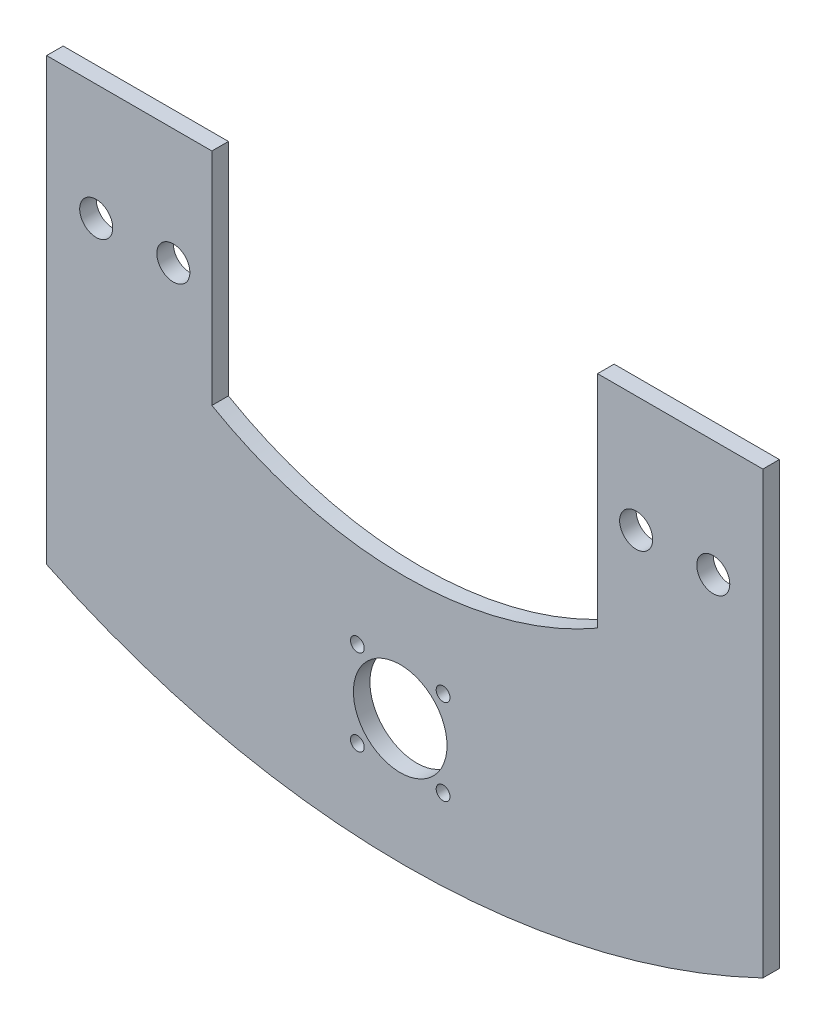
SolidWorks part; units mm, degrees
ref_plane "Front Plane" through (0, 0, 0) normal (0, 0, 1) x (1, 0, 0)
ref_plane "Top Plane" through (0, 0, 0) normal (0, 1, 0) x (1, 0, 0)
ref_plane "Right Plane" through (0, 0, 0) normal (1, 0, 0) x (0, 0, -1)
sketch "Sketch1" plane through (0, 0, 0) normal (0, 0, 1) x (1, 0, 0)
  line L1 (-34.1797, 1.6565) -> (-34.1797, 41.6565)
  line L2 (-34.1797, 41.6565) -> (-64.1797, 41.6565)
  line L3 (-64.1797, 41.6565) -> (-64.1797, -38.3435)
  line L5 (65.8203, -38.3435) -> (65.8203, 41.6565)
  line L6 (65.8203, 41.6565) -> (35.8203, 41.6565)
  line L7 (35.8203, 41.6565) -> (35.8203, 1.6565)
  arc A0 (-34.1797, 1.6565) -> (35.8203, 1.6565) centre (0.8203, 62.2783) ccw
  arc A1 (-64.1797, -38.3435) -> (65.8203, -38.3435) centre (0.8203, 96.8416) ccw
  circle A2 centre (56.8203, 20.5545) radius 3
  circle A3 centre (42.8203, 20.5545) radius 3
  circle A4 centre (-55.1797, 20.5545) radius 3
  circle A5 centre (-41.1797, 20.5545) radius 3
  point P4 (0, 0)
  dimension "D7" = 70
  dimension "D8" = 150
  dimension "D9" = 6
  dimension "D10" = 6
  dimension "D1" = 130
  dimension "D2" = 30
  dimension "D3" = 30
  dimension "D4" = 40
  dimension "D5" = 40
  dimension "D6" = 80
  dimension "D11" = 9
  dimension "D12" = 14
  dimension "D13" = 84
  dimension "D14" = 14
  dimension "D15" = 80
extrude "Boss-Extrude2" add sketch "Sketch1" along normal blind 3
sketch "Sketch4" plane through (0, 0, 3) normal (0, 0, 1) x (1, 0, 0)
  circle A0 centre (7.78, -22.6969) radius 1.25
  circle A1 centre (7.78, -38.2569) radius 1.25
  circle A2 centre (-7.78, -38.2569) radius 1.25
  circle A3 centre (-7.78, -22.6969) radius 1.25
  circle A4 centre (0, -30.4769) radius 8.5
  point P0 (0, -30.4769)
  dimension "D3" = 2.5
  dimension "D4" = 17
  dimension "D1" = 15.56
  dimension "D2" = 15.56
extrude "Cut-Extrude2" cut sketch "Sketch4" against normal blind 10
